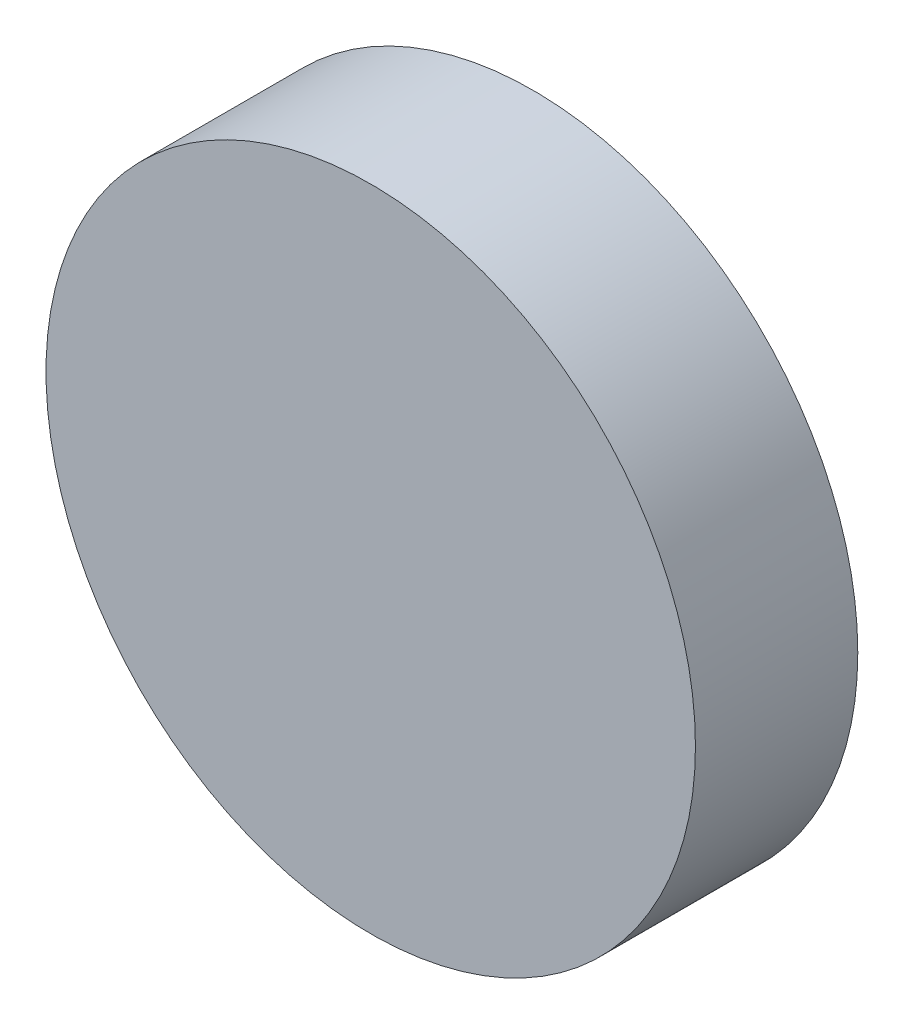
SolidWorks part; units mm, degrees
ref_plane "Front Plane" through (0, 0, 0) normal (0, 0, 1) x (1, 0, 0)
ref_plane "Top Plane" through (0, 0, 0) normal (0, 1, 0) x (1, 0, 0)
ref_plane "Right Plane" through (0, 0, 0) normal (1, 0, 0) x (0, 0, -1)
sketch "Sketch1" plane through (0, 0, 0) normal (0, 0, 1) x (1, 0, 0)
  circle A0 centre (0, 0) radius 20
extrude "Boss-Extrude1" add sketch "Sketch1" along normal blind 10
